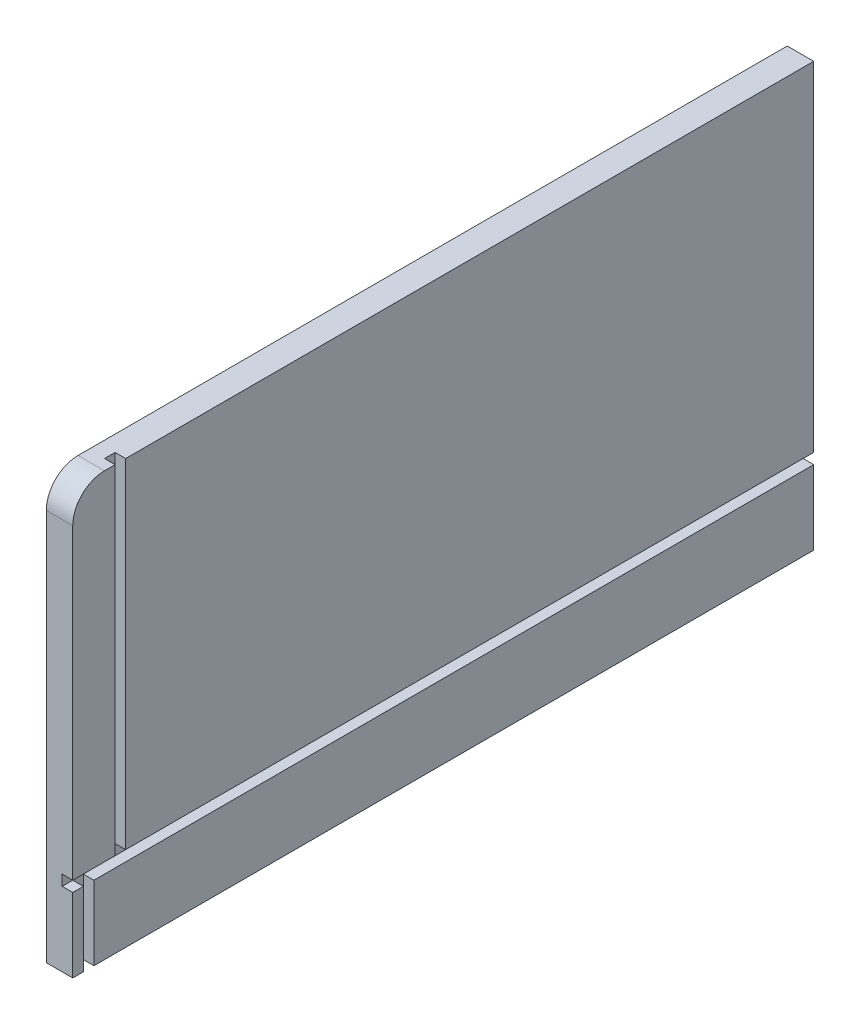
SolidWorks part; units mm, degrees
ref_plane "Front Plane" through (0, 0, 0) normal (0, 0, 1) x (1, 0, 0)
ref_plane "Top Plane" through (0, 0, 0) normal (0, 1, 0) x (1, 0, 0)
ref_plane "Right Plane" through (0, 0, 0) normal (1, 0, 0) x (0, 0, -1)
sketch "Sketch1" plane through (0, 0, 0) normal (1, 0, 0) x (0, 0, -1)
  line L1 (0, 0) -> (444.5, 0)
  line L2 (0, 0) -> (0, 234.95)
  line L3 (19.05, 254) -> (444.5, 254)
  line L4 (444.5, 0) -> (444.5, 254)
  arc A0 (0, 234.95) -> (19.05, 254) centre (19.05, 234.95) cw
  point P7 (444.5, 254)
  point P8 (0, 254)
  dimension "D3" = 19.05
  dimension "D1" = 444.5
  dimension "D2" = 254
extrude "Boss-Extrude1" add sketch "Sketch1" along normal blind 15.875
sketch "Sketch2" plane through (0, 0, -444.5) normal (0, 0, -1) x (-1, 0, 0)
  line L0 (-15.875, 0) -> (-15.875, 254) construction
  line L1 (-15.875, 50.8) -> (-9.525, 50.8)
  line L2 (-15.875, 50.8) -> (-15.875, 44.45)
  line L3 (-15.875, 44.45) -> (-9.525, 44.45)
  line L4 (-9.525, 50.8) -> (-9.525, 44.45)
  line L5 (-15.875, 254) -> (0, 254) construction
  dimension "D1" = 6.35
  dimension "D2" = 6.35
  dimension "D3" = 203.2
extrude "Cut-Extrude1" cut sketch "Sketch2" against normal through all
sketch "Sketch3" plane through (0, 0, 0) normal (0, -1, 0) x (1, 0, 0)
  line L0 (15.875, 0) -> (15.875, -444.5) construction
  line L1 (15.875, -6.35) -> (9.525, -6.35)
  line L2 (15.875, -6.35) -> (15.875, -12.7)
  line L3 (15.875, -12.7) -> (9.525, -12.7)
  line L4 (9.525, -6.35) -> (9.525, -12.7)
  line L5 (15.875, 0) -> (0, 0) construction
  dimension "D1" = 6.35
  dimension "D2" = 6.35
  dimension "D3" = 6.35
extrude "Cut-Extrude3" cut sketch "Sketch3" against normal up to next
sketch "Sketch4" plane through (0, 254, 0) normal (0, 1, 0) x (1, 0, 0)
  line L0 (15.875, 444.5) -> (15.875, 19.05) construction
  line L1 (15.875, 25.4) -> (9.525, 25.4)
  line L2 (15.875, 25.4) -> (15.875, 31.75)
  line L3 (15.875, 31.75) -> (9.525, 31.75)
  line L4 (9.525, 25.4) -> (9.525, 31.75)
  line L5 (15.875, 19.05) -> (0, 19.05) construction
  dimension "D1" = 6.35
  dimension "D2" = 6.35
  dimension "D3" = 6.35
extrude "Cut-Extrude4" cut sketch "Sketch4" against normal up to next
